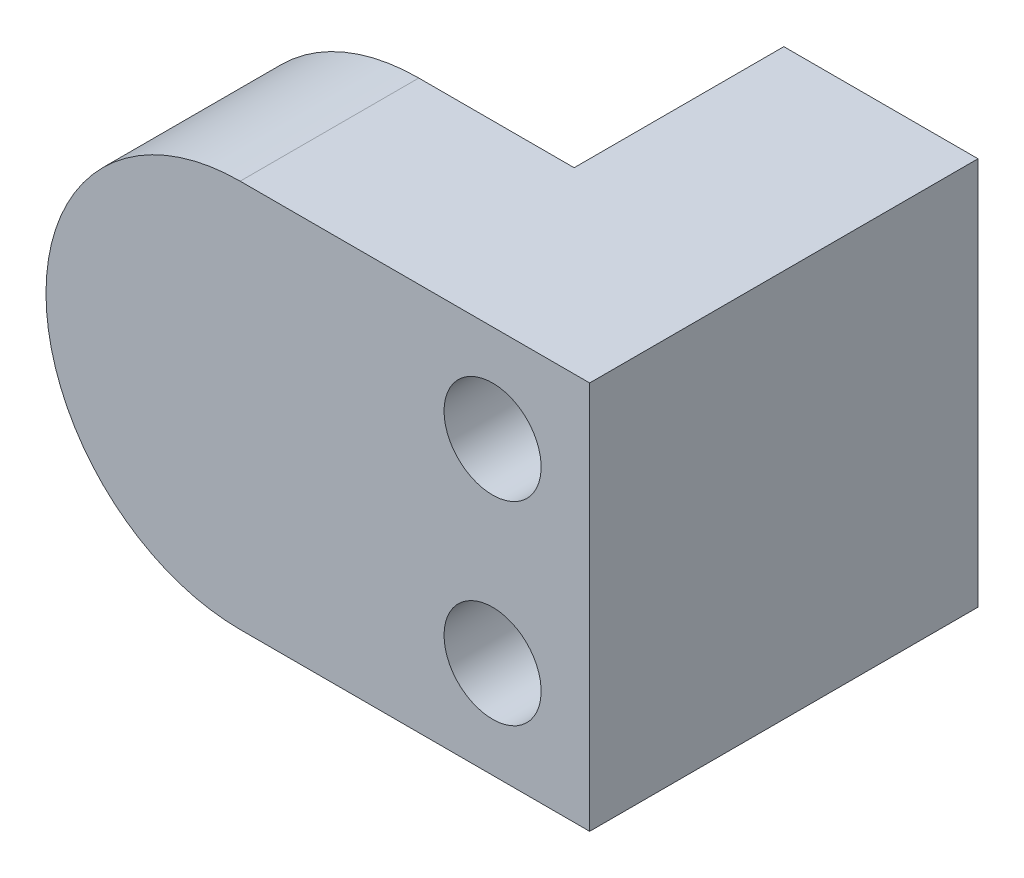
SolidWorks part; units mm, degrees
ref_plane "Front Plane" through (0, 0, 0) normal (0, 0, 1) x (1, 0, 0)
ref_plane "Top Plane" through (0, 0, 0) normal (0, 1, 0) x (1, 0, 0)
ref_plane "Right Plane" through (0, 0, 0) normal (1, 0, 0) x (0, 0, -1)
sketch "Sketch1" plane through (0, 0, 0) normal (0, 0, 1) x (1, 0, 0)
  line L1 (-3.175, -6.35) -> (3.175, -6.35)
  line L2 (-3.175, -6.35) -> (-3.175, 6.35)
  line L3 (-3.175, 6.35) -> (3.175, 6.35)
  line L4 (3.175, -6.35) -> (3.175, 6.35)
  line L5 (-3.175, -6.35) -> (3.175, 6.35) construction
  line L6 (-3.175, 6.35) -> (3.175, -6.35) construction
  point P0 (0, 0)
  dimension "D1" = 6.35
  dimension "D2" = 12.7
extrude "Boss-Extrude1" add sketch "Sketch1" along normal blind 13.208
sketch "Sketch2" plane through (-3.175, 0, 0) normal (-1, 0, 0) x (0, 0, 1)
  line L0 (13.208, 6.35) -> (0, 6.35) construction
  line L1 (13.208, -6.35) -> (6.858, -6.35)
  line L2 (13.208, -6.35) -> (13.208, 6.35)
  line L3 (13.208, 6.35) -> (6.858, 6.35)
  line L4 (6.858, -6.35) -> (6.858, 6.35)
  dimension "D1" = 6.35
extrude "Boss-Extrude2" add sketch "Sketch2" along normal blind 5.08
sketch "Sketch3" plane through (0, 0, 13.208) normal (0, 0, 1) x (1, 0, 0)
  line L0 (-8.255, -6.35) -> (-8.255, 6.35) construction
  circle A1 centre (-8.255, 0) radius 6.35
  dimension "D1" = 12.7
extrude "Boss-Extrude3" add sketch "Sketch3" against normal up to surface (6.35 mm away) up to face at (-5.715, 0, 6.858)
sketch "Sketch4" plane through (0, 0, 0) normal (0, 0, -1) x (-1, 0, 0)
  line L0 (0, 0) -> (3.175, 0) construction
  line L1 (3.175, 6.35) -> (3.175, -6.35) construction
  line L2 (-3.175, 6.35) -> (3.175, 6.35) construction
  line L3 (3.175, 6.35) -> (3.175, -6.35) construction
  circle A0 centre (0, 3.175) radius 1.5875
  circle A1 centre (0, -3.175) radius 1.5875
  point P9 (0, 0)
  point P10 (0, 0)
  dimension "D1" = 3.175
  dimension "D2" = 1.5875
  dimension "D3" = 1.5875
extrude "Cut-Extrude1" cut sketch "Sketch4" against normal up to surface (13.208 mm away) up to face at (-4.1275, 0, 13.208)
other "Move Face1" face at (-1.5875, 3.175, 13.208) parameters "D1"=0.508
